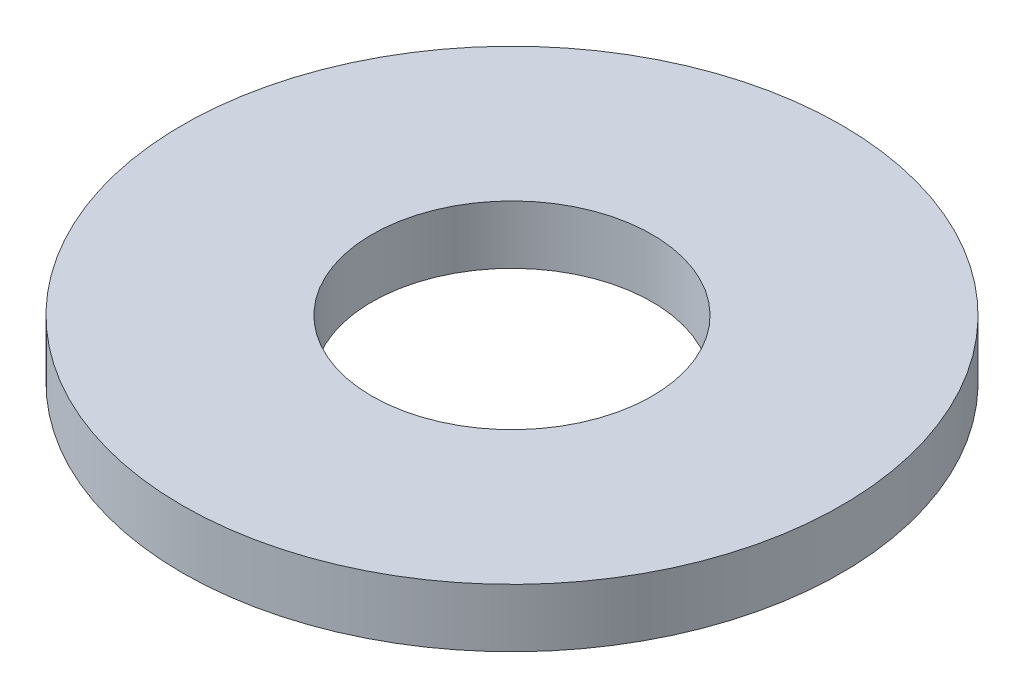
SolidWorks part; units mm, degrees
material "Plain Carbon Steel"
ref_plane "Front Plane" through (0, 0, 0) normal (0, 0, 1) x (1, 0, 0)
ref_plane "Top Plane" through (0, 0, 0) normal (0, 1, 0) x (1, 0, 0)
ref_plane "Right Plane" through (0, 0, 0) normal (1, 0, 0) x (0, 0, -1)
sketch "Sketch1" plane through (0, 0, 0) normal (0, 1, 0) x (1, 0, 0)
  circle A0 centre (0, 0) radius 3.9624
  circle A1 centre (0, 0) radius 9.3218
  dimension "D1" = 7.9248
  dimension "D2" = 18.6436
extrude "Boss-Extrude1" add sketch "Sketch1" along normal blind 1.651
